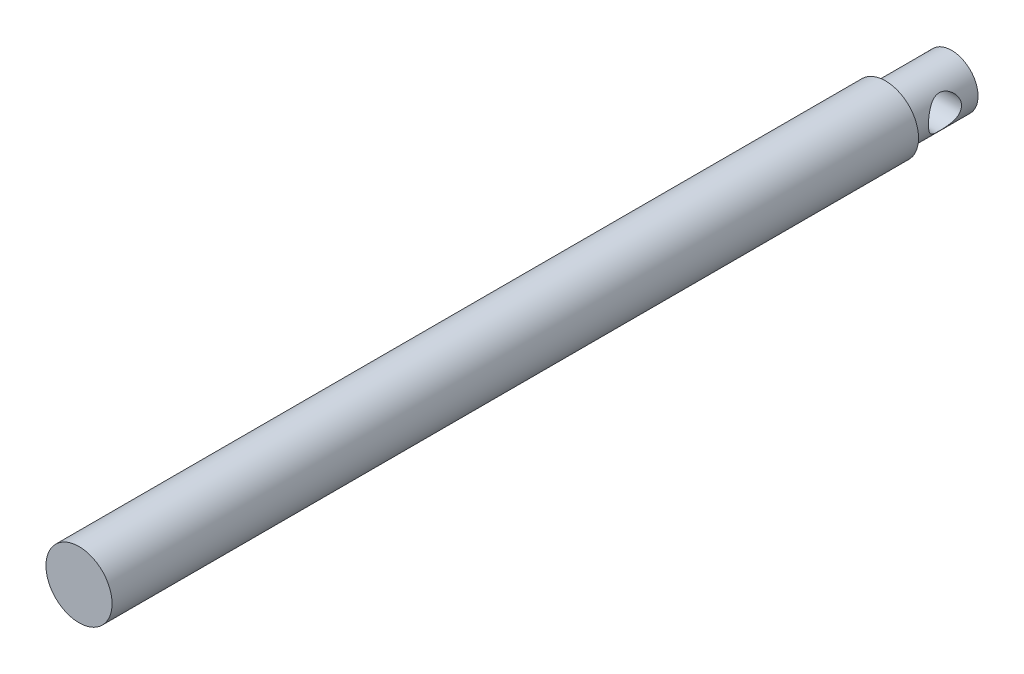
SolidWorks part; units mm, degrees
ref_plane "Front Plane" through (0, 0, 0) normal (0, 0, 1) x (1, 0, 0)
ref_plane "Top Plane" through (0, 0, 0) normal (0, 1, 0) x (1, 0, 0)
ref_plane "Right Plane" through (0, 0, 0) normal (1, 0, 0) x (0, 0, -1)
sketch "Sketch1" plane through (0, 0, 0) normal (0, 0, 1) x (1, 0, 0)
  circle A0 centre (0, 0) radius 5
  dimension "D1" = 10
extrude "Boss-Extrude1" add sketch "Sketch1" along normal blind 122
sketch "Sketch2" plane through (0, 0, 0) normal (0, 0, -1) x (-1, 0, 0)
  circle A0 centre (0, 0) radius 4
  dimension "D1" = 8
extrude "Boss-Extrude2" add sketch "Sketch2" along normal blind 10
sketch "Sketch3" plane through (0, 0, 0) normal (1, 0, 0) x (0, 0, -1)
  line L0 (10, -4) -> (10, 4) construction
  circle A0 centre (5, 0) radius 2.5
  dimension "D1" = 5
  dimension "D2" = 5
extrude "Cut-Extrude1" cut sketch "Sketch3" against normal through all both and the other way through all
